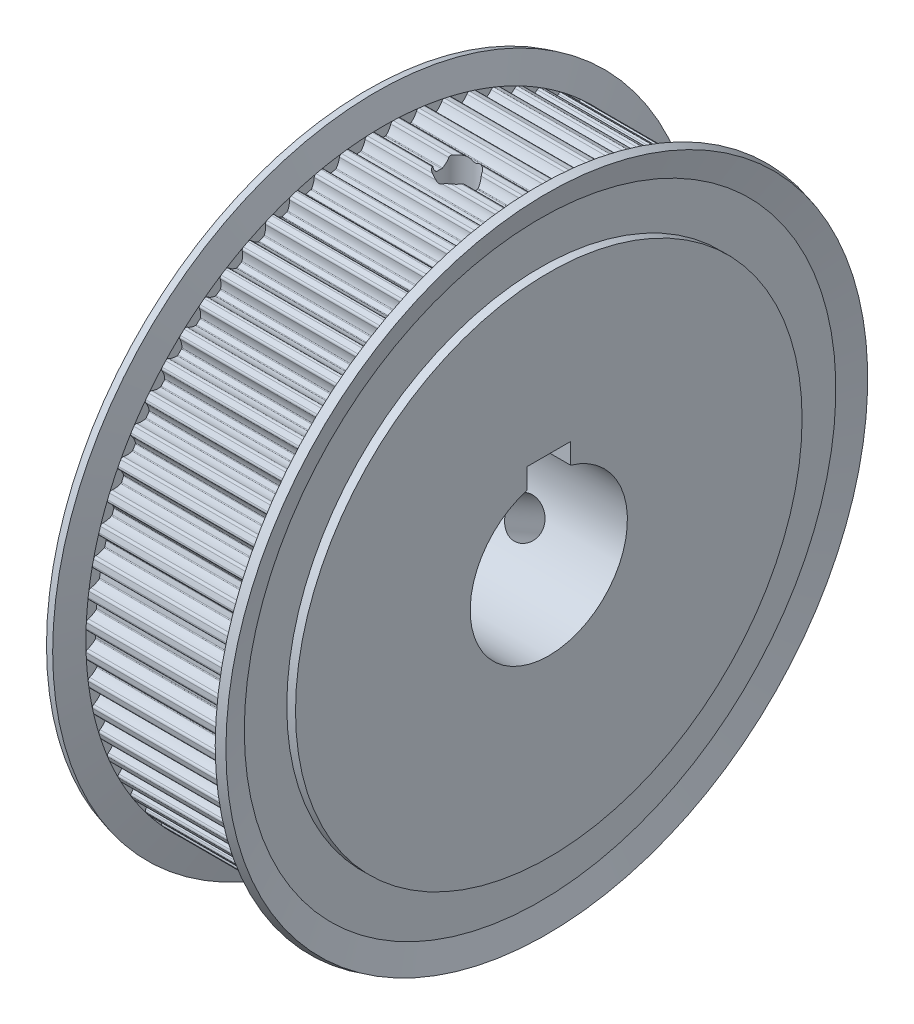
SolidWorks part; units mm, degrees
ref_plane "正面" through (0, 0, 0) normal (0, 0, 1) x (1, 0, 0)
ref_plane "平面" through (0, 0, 0) normal (0, 1, 0) x (1, 0, 0)
ref_plane "右側面" through (0, 0, 0) normal (1, 0, 0) x (0, 0, -1)
ref_plane "平面1" through (0, 0, 0) normal (0, 0, 1) x (1, 0, 0)
sketch "ｽｹｯﾁ1" plane through (0, 0, 0) normal (0, 0, 1) x (1, 0, 0)
  line L0 (0, 0) -> (0, 29)
  line L1 (0, 29) -> (1, 29)
  line L2 (1, 29) -> (1, 33.8633)
  line L3 (1, 33.8633) -> (0.2289, 36.7412)
  line L4 (0.2289, 36.7412) -> (1.1948, 37)
  line L5 (1.1948, 37) -> (2, 33.995)
  line L6 (2, 33.995) -> (19, 33.995)
  line L7 (19, 33.995) -> (19.8052, 37)
  line L8 (19.8052, 37) -> (20.7711, 36.7412)
  line L9 (20.7711, 36.7412) -> (20, 33.8633)
  line L10 (20, 33.8633) -> (20, 29)
  line L11 (20, 29) -> (21, 29)
  line L12 (21, 29) -> (21, 0)
  line L13 (21, 0) -> (0, 0)
  line L14 (21, 0) -> (0, 0) construction
revolve "回転1" add sketch "ｽｹｯﾁ1" angle 360 about L14
ref_plane "平面2" through (0, 0, 0) normal (0, 0, 1) x (1, 0, 0)
sketch "ｽｹｯﾁ2" plane through (0, 0, 0) normal (0, 0, 1) x (1, 0, 0)
  line L0 (0, 0) -> (0, 9)
  line L1 (0, 9) -> (21, 9)
  line L2 (21, 9) -> (21, 0)
  line L3 (21, 0) -> (0, 0)
  line L4 (21, 0) -> (0, 0) construction
revolve "ｶｯﾄ - 回転1" cut sketch "ｽｹｯﾁ2" angle 360 about L4
ref_plane "平面3" through (2, 0, 0) normal (1, 0, 0) x (0, 0, -1)
sketch "ｽｹｯﾁ3" plane through (2, 0, 0) normal (1, 0, 0) x (0, 0, -1)
  circle A0 centre (0, 0) radius 38.995
  arc A1 (-33.7772, -0.9117) -> (-33.9742, -1.189) centre (-33.6944, -1.1792) ccw
  arc A2 (-33.9742, -1.189) -> (-33.9485, -1.7766) centre (0, 0) ccw
  arc A3 (-33.9485, -1.7766) -> (-33.7281, -2.0357) centre (-33.6689, -1.762) ccw
  arc A4 (-33.7281, -2.0357) -> (-32.8326, -2.4906) centre (-34.1454, -3.9661) cw
  arc A5 (-32.8326, -2.4906) -> (-32.7828, -2.5908) centre (-32.9323, -2.6026) cw
  arc A6 (-32.7828, -2.5908) -> (-32.7346, -3.1412) centre (0, 0) ccw
  arc A7 (-32.7346, -3.1412) -> (-32.7663, -3.2486) centre (-32.8839, -3.1556) cw
  arc A8 (-32.7663, -3.2486) -> (-33.5692, -3.8521) centre (-34.3154, -2.0235) cw
  arc A9 (-33.5692, -3.8521) -> (-33.7413, -4.1455) centre (-33.4634, -4.1113) ccw
  arc A10 (-33.7413, -4.1455) -> (-33.6645, -4.7287) centre (0, 0) ccw
  arc A11 (-33.6645, -4.7287) -> (-33.4223, -4.9675) centre (-33.3872, -4.6897) ccw
  arc A12 (-33.4223, -4.9675) -> (-32.4906, -5.3426) centre (-33.6698, -6.9269) cw
  arc A13 (-32.4906, -5.3426) -> (-32.4322, -5.4382) centre (-32.5802, -5.463) cw
  arc A14 (-32.4322, -5.4382) -> (-32.3363, -5.9823) centre (0, 0) ccw
  arc A15 (-32.3363, -5.9823) -> (-32.3585, -6.092) centre (-32.4838, -6.0096) cw
  arc A16 (-32.3585, -6.092) -> (-33.1057, -6.7632) centre (-34.0085, -5.0066) cw
  arc A17 (-33.1057, -6.7632) -> (-33.2516, -7.0704) centre (-32.9777, -7.0122) ccw
  arc A18 (-33.2516, -7.0704) -> (-33.1243, -7.6447) centre (0, 0) ccw
  arc A19 (-33.1243, -7.6447) -> (-32.8622, -7.8616) centre (-32.8515, -7.5818) ccw
  arc A20 (-32.8622, -7.8616) -> (-31.9013, -8.154) centre (-32.938, -9.8351) cw
  arc A21 (-31.9013, -8.154) -> (-31.8349, -8.2441) centre (-31.9801, -8.2817) cw
  arc A22 (-31.8349, -8.2441) -> (-31.6918, -8.7778) centre (0, 0) ccw
  arc A23 (-31.6918, -8.7778) -> (-31.7044, -8.8891) centre (-31.8364, -8.8178) cw
  arc A24 (-31.7044, -8.8891) -> (-32.3903, -9.6228) centre (-33.4427, -7.9515) cw
  arc A25 (-32.3903, -9.6228) -> (-32.5088, -9.9416) centre (-32.2411, -9.8597) ccw
  arc A26 (-32.5088, -9.9416) -> (-32.332, -10.5026) centre (0, 0) ccw
  arc A27 (-32.332, -10.5026) -> (-32.052, -10.6958) centre (-32.0657, -10.4161) ccw
  arc A28 (-32.052, -10.6958) -> (-31.0693, -10.9034) centre (-31.9555, -12.6684) cw
  arc A29 (-31.0693, -10.9034) -> (-30.9952, -10.9873) centre (-31.1366, -11.0375) cw
  arc A30 (-30.9952, -10.9873) -> (-30.8062, -11.5065) centre (0, 0) ccw
  arc A31 (-30.8062, -11.5065) -> (-30.809, -11.6184) centre (-30.9467, -11.559) cw
  arc A32 (-30.809, -11.6184) -> (-31.4283, -12.4092) centre (-32.6224, -10.836) cw
  arc A33 (-31.4283, -12.4092) -> (-31.5187, -12.7371) centre (-31.2591, -12.6322) ccw
  arc A34 (-31.5187, -12.7371) -> (-31.2936, -13.2806) centre (0, 0) ccw
  arc A35 (-31.2936, -13.2806) -> (-30.9978, -13.4486) centre (-31.0358, -13.1712) ccw
  arc A36 (-30.9978, -13.4486) -> (-30.0007, -13.5698) centre (-30.7297, -15.4053) cw
  arc A37 (-30.0007, -13.5698) -> (-29.9196, -13.6469) centre (-30.0561, -13.7092) cw
  arc A38 (-29.9196, -13.6469) -> (-29.6861, -14.1477) centre (0, 0) ccw
  arc A39 (-29.6861, -14.1477) -> (-29.6792, -14.2594) centre (-29.8215, -14.2122) cw
  arc A40 (-29.6792, -14.2594) -> (-30.2272, -15.1011) centre (-31.5538, -13.638) cw
  arc A41 (-30.2272, -15.1011) -> (-30.2886, -15.4357) centre (-30.0391, -15.3085) ccw
  arc A42 (-30.2886, -15.4357) -> (-30.017, -15.9574) centre (0, 0) ccw
  arc A43 (-30.017, -15.9574) -> (-29.7077, -16.099) centre (-29.7698, -15.826) ccw
  arc A44 (-29.7077, -16.099) -> (-28.7039, -16.1329) centre (-29.2701, -18.025) cw
  arc A45 (-28.7039, -16.1329) -> (-28.6164, -16.2027) centre (-28.7469, -16.2766) cw
  arc A46 (-28.6164, -16.2027) -> (-28.3401, -16.6812) centre (0, 0) ccw
  arc A47 (-28.3401, -16.6812) -> (-28.3234, -16.7919) centre (-28.4694, -16.7573) cw
  arc A48 (-28.3234, -16.7919) -> (-28.796, -17.6781) centre (-30.2451, -16.3362) cw
  arc A49 (-28.796, -17.6781) -> (-28.828, -18.0168) centre (-28.5906, -17.8684) ccw
  arc A50 (-28.828, -18.0168) -> (-28.512, -18.5129) centre (0, 0) ccw
  arc A51 (-28.512, -18.5129) -> (-28.1916, -18.627) centre (-28.2772, -18.3604) ccw
  arc A52 (-28.1916, -18.627) -> (-27.1886, -18.5732) centre (-27.5878, -20.5074) cw
  arc A53 (-27.1886, -18.5732) -> (-27.0953, -18.6351) centre (-27.2189, -18.7201) cw
  arc A54 (-27.0953, -18.6351) -> (-26.7784, -19.0877) centre (0, 0) ccw
  arc A55 (-26.7784, -19.0877) -> (-26.7521, -19.1965) centre (-26.9006, -19.1748) cw
  arc A56 (-26.7521, -19.1965) -> (-27.1457, -20.1206) centre (-28.7063, -18.9101) cw
  arc A57 (-27.1457, -20.1206) -> (-27.1481, -20.4607) centre (-26.9245, -20.2922) ccw
  arc A58 (-27.1481, -20.4607) -> (-26.79, -20.9274) centre (0, 0) ccw
  arc A59 (-26.79, -20.9274) -> (-26.4608, -21.0132) centre (-26.5693, -20.755) ccw
  arc A60 (-26.4608, -21.0132) -> (-25.4664, -20.8722) centre (-25.6955, -22.8338) cw
  arc A61 (-25.4664, -20.8722) -> (-25.3681, -20.9257) centre (-25.4838, -21.0211) cw
  arc A62 (-25.3681, -20.9257) -> (-25.0129, -21.349) centre (0, 0) ccw
  arc A63 (-25.0129, -21.349) -> (-24.9773, -21.4551) centre (-25.127, -21.4463) cw
  arc A64 (-24.9773, -21.4551) -> (-25.2888, -22.4099) centre (-26.9489, -21.34) cw
  arc A65 (-25.2888, -22.4099) -> (-25.2615, -22.749) centre (-25.0534, -22.5616) ccw
  arc A66 (-25.2615, -22.749) -> (-24.8641, -23.1827) centre (0, 0) ccw
  arc A67 (-24.8641, -23.1827) -> (-24.5287, -23.2394) centre (-24.6593, -22.9917) ccw
  arc A68 (-24.5287, -23.2394) -> (-23.5503, -23.0123) centre (-23.6076, -24.9864) cw
  arc A69 (-23.5503, -23.0123) -> (-23.4477, -23.057) centre (-23.5547, -23.1622) cw
  arc A70 (-23.4477, -23.057) -> (-23.057, -23.4477) centre (0, 0) ccw
  arc A71 (-23.057, -23.4477) -> (-23.0123, -23.5503) centre (-23.1622, -23.5547) cw
  arc A72 (-23.0123, -23.5503) -> (-23.2394, -24.5287) centre (-24.9864, -23.6076) cw
  arc A73 (-23.2394, -24.5287) -> (-23.1827, -24.8641) centre (-22.9917, -24.6593) ccw
  arc A74 (-23.1827, -24.8641) -> (-22.749, -25.2615) centre (0, 0) ccw
  arc A75 (-22.749, -25.2615) -> (-22.4099, -25.2888) centre (-22.5616, -25.0534) ccw
  arc A76 (-22.4099, -25.2888) -> (-21.4551, -24.9773) centre (-21.34, -26.9489) cw
  arc A77 (-21.4551, -24.9773) -> (-21.349, -25.0129) centre (-21.4463, -25.127) cw
  arc A78 (-21.349, -25.0129) -> (-20.9257, -25.3681) centre (0, 0) ccw
  arc A79 (-20.9257, -25.3681) -> (-20.8722, -25.4664) centre (-21.0211, -25.4838) cw
  arc A80 (-20.8722, -25.4664) -> (-21.0132, -26.4608) centre (-22.8338, -25.6955) cw
  arc A81 (-21.0132, -26.4608) -> (-20.9274, -26.79) centre (-20.755, -26.5693) ccw
  arc A82 (-20.9274, -26.79) -> (-20.4607, -27.1481) centre (0, 0) ccw
  arc A83 (-20.4607, -27.1481) -> (-20.1206, -27.1457) centre (-20.2922, -26.9245) ccw
  arc A84 (-20.1206, -27.1457) -> (-19.1965, -26.7521) centre (-18.9101, -28.7063) cw
  arc A85 (-19.1965, -26.7521) -> (-19.0877, -26.7784) centre (-19.1748, -26.9006) cw
  arc A86 (-19.0877, -26.7784) -> (-18.6351, -27.0953) centre (0, 0) ccw
  arc A87 (-18.6351, -27.0953) -> (-18.5732, -27.1886) centre (-18.7201, -27.2189) cw
  arc A88 (-18.5732, -27.1886) -> (-18.627, -28.1916) centre (-20.5074, -27.5878) cw
  arc A89 (-18.627, -28.1916) -> (-18.5129, -28.512) centre (-18.3604, -28.2772) ccw
  arc A90 (-18.5129, -28.512) -> (-18.0168, -28.828) centre (0, 0) ccw
  arc A91 (-18.0168, -28.828) -> (-17.6781, -28.796) centre (-17.8684, -28.5906) ccw
  arc A92 (-17.6781, -28.796) -> (-16.7919, -28.3234) centre (-16.3362, -30.2451) cw
  arc A93 (-16.7919, -28.3234) -> (-16.6812, -28.3401) centre (-16.7573, -28.4694) cw
  arc A94 (-16.6812, -28.3401) -> (-16.2027, -28.6164) centre (0, 0) ccw
  arc A95 (-16.2027, -28.6164) -> (-16.1329, -28.7039) centre (-16.2766, -28.7469) cw
  arc A96 (-16.1329, -28.7039) -> (-16.099, -29.7077) centre (-18.025, -29.2701) cw
  arc A97 (-16.099, -29.7077) -> (-15.9574, -30.017) centre (-15.826, -29.7698) ccw
  arc A98 (-15.9574, -30.017) -> (-15.4357, -30.2886) centre (0, 0) ccw
  arc A99 (-15.4357, -30.2886) -> (-15.1011, -30.2272) centre (-15.3085, -30.0391) ccw
  arc A100 (-15.1011, -30.2272) -> (-14.2594, -29.6792) centre (-13.638, -31.5538) cw
  arc A101 (-14.2594, -29.6792) -> (-14.1477, -29.6861) centre (-14.2122, -29.8215) cw
  arc A102 (-14.1477, -29.6861) -> (-13.6469, -29.9196) centre (0, 0) ccw
  arc A103 (-13.6469, -29.9196) -> (-13.5698, -30.0007) centre (-13.7092, -30.0561) cw
  arc A104 (-13.5698, -30.0007) -> (-13.4486, -30.9978) centre (-15.4053, -30.7297) cw
  arc A105 (-13.4486, -30.9978) -> (-13.2806, -31.2936) centre (-13.1712, -31.0358) ccw
  arc A106 (-13.2806, -31.2936) -> (-12.7371, -31.5187) centre (0, 0) ccw
  arc A107 (-12.7371, -31.5187) -> (-12.4092, -31.4283) centre (-12.6322, -31.2591) ccw
  arc A108 (-12.4092, -31.4283) -> (-11.6184, -30.809) centre (-10.836, -32.6224) cw
  arc A109 (-11.6184, -30.809) -> (-11.5065, -30.8062) centre (-11.559, -30.9467) cw
  arc A110 (-11.5065, -30.8062) -> (-10.9873, -30.9952) centre (0, 0) ccw
  arc A111 (-10.9873, -30.9952) -> (-10.9034, -31.0693) centre (-11.0375, -31.1366) cw
  arc A112 (-10.9034, -31.0693) -> (-10.6958, -32.052) centre (-12.6684, -31.9555) cw
  arc A113 (-10.6958, -32.052) -> (-10.5026, -32.332) centre (-10.4161, -32.0657) ccw
  arc A114 (-10.5026, -32.332) -> (-9.9416, -32.5088) centre (0, 0) ccw
  arc A115 (-9.9416, -32.5088) -> (-9.6228, -32.3903) centre (-9.8597, -32.2411) ccw
  arc A116 (-9.6228, -32.3903) -> (-8.8891, -31.7044) centre (-7.9515, -33.4427) cw
  arc A117 (-8.8891, -31.7044) -> (-8.7778, -31.6918) centre (-8.8178, -31.8364) cw
  arc A118 (-8.7778, -31.6918) -> (-8.2441, -31.8349) centre (0, 0) ccw
  arc A119 (-8.2441, -31.8349) -> (-8.154, -31.9013) centre (-8.2817, -31.9801) cw
  arc A120 (-8.154, -31.9013) -> (-7.8616, -32.8622) centre (-9.8351, -32.938) cw
  arc A121 (-7.8616, -32.8622) -> (-7.6447, -33.1243) centre (-7.5818, -32.8515) ccw
  arc A122 (-7.6447, -33.1243) -> (-7.0704, -33.2516) centre (0, 0) ccw
  arc A123 (-7.0704, -33.2516) -> (-6.7632, -33.1057) centre (-7.0122, -32.9777) ccw
  arc A124 (-6.7632, -33.1057) -> (-6.092, -32.3585) centre (-5.0066, -34.0085) cw
  arc A125 (-6.092, -32.3585) -> (-5.9823, -32.3363) centre (-6.0096, -32.4838) cw
  arc A126 (-5.9823, -32.3363) -> (-5.4382, -32.4322) centre (0, 0) ccw
  arc A127 (-5.4382, -32.4322) -> (-5.3426, -32.4906) centre (-5.463, -32.5802) cw
  arc A128 (-5.3426, -32.4906) -> (-4.9675, -33.4223) centre (-6.9269, -33.6698) cw
  arc A129 (-4.9675, -33.4223) -> (-4.7287, -33.6645) centre (-4.6897, -33.3872) ccw
  arc A130 (-4.7287, -33.6645) -> (-4.1455, -33.7413) centre (0, 0) ccw
  arc A131 (-4.1455, -33.7413) -> (-3.8521, -33.5692) centre (-4.1113, -33.4634) ccw
  arc A132 (-3.8521, -33.5692) -> (-3.2486, -32.7663) centre (-2.0235, -34.3154) cw
  arc A133 (-3.2486, -32.7663) -> (-3.1412, -32.7346) centre (-3.1556, -32.8839) cw
  arc A134 (-3.1412, -32.7346) -> (-2.5908, -32.7828) centre (0, 0) ccw
  arc A135 (-2.5908, -32.7828) -> (-2.4906, -32.8326) centre (-2.6026, -32.9323) cw
  arc A136 (-2.4906, -32.8326) -> (-2.0357, -33.7281) centre (-3.9661, -34.1454) cw
  arc A137 (-2.0357, -33.7281) -> (-1.7766, -33.9485) centre (-1.762, -33.6689) ccw
  arc A138 (-1.7766, -33.9485) -> (-1.189, -33.9742) centre (0, 0) ccw
  arc A139 (-1.189, -33.9742) -> (-0.9117, -33.7772) centre (-1.1792, -33.6944) ccw
  arc A140 (-0.9117, -33.7772) -> (-0.3805, -32.9247) centre (0.975, -34.3612) cw
  arc A141 (-0.3805, -32.9247) -> (-0.2763, -32.8838) centre (-0.2775, -33.0338) cw
  arc A142 (-0.2763, -32.8838) -> (0.2763, -32.8838) centre (0, 0) ccw
  arc A143 (0.2763, -32.8838) -> (0.3805, -32.9247) centre (0.2775, -33.0338) cw
  arc A144 (0.3805, -32.9247) -> (0.9117, -33.7772) centre (-0.975, -34.3612) cw
  arc A145 (0.9117, -33.7772) -> (1.189, -33.9742) centre (1.1792, -33.6944) ccw
  arc A146 (1.189, -33.9742) -> (1.7766, -33.9485) centre (0, 0) ccw
  arc A147 (1.7766, -33.9485) -> (2.0357, -33.7281) centre (1.762, -33.6689) ccw
  arc A148 (2.0357, -33.7281) -> (2.4906, -32.8326) centre (3.9661, -34.1454) cw
  arc A149 (2.4906, -32.8326) -> (2.5908, -32.7828) centre (2.6026, -32.9323) cw
  arc A150 (2.5908, -32.7828) -> (3.1412, -32.7346) centre (0, 0) ccw
  arc A151 (3.1412, -32.7346) -> (3.2486, -32.7663) centre (3.1556, -32.8839) cw
  arc A152 (3.2486, -32.7663) -> (3.8521, -33.5692) centre (2.0235, -34.3154) cw
  arc A153 (3.8521, -33.5692) -> (4.1455, -33.7413) centre (4.1113, -33.4634) ccw
  arc A154 (4.1455, -33.7413) -> (4.7287, -33.6645) centre (0, 0) ccw
  arc A155 (4.7287, -33.6645) -> (4.9675, -33.4223) centre (4.6897, -33.3872) ccw
  arc A156 (4.9675, -33.4223) -> (5.3426, -32.4906) centre (6.9269, -33.6698) cw
  arc A157 (5.3426, -32.4906) -> (5.4382, -32.4322) centre (5.463, -32.5802) cw
  arc A158 (5.4382, -32.4322) -> (5.9823, -32.3363) centre (0, 0) ccw
  arc A159 (5.9823, -32.3363) -> (6.092, -32.3585) centre (6.0096, -32.4838) cw
  arc A160 (6.092, -32.3585) -> (6.7632, -33.1057) centre (5.0066, -34.0085) cw
  arc A161 (6.7632, -33.1057) -> (7.0704, -33.2516) centre (7.0122, -32.9777) ccw
  arc A162 (7.0704, -33.2516) -> (7.6447, -33.1243) centre (0, 0) ccw
  arc A163 (7.6447, -33.1243) -> (7.8616, -32.8622) centre (7.5818, -32.8515) ccw
  arc A164 (7.8616, -32.8622) -> (8.154, -31.9013) centre (9.8351, -32.938) cw
  arc A165 (8.154, -31.9013) -> (8.2441, -31.8349) centre (8.2817, -31.9801) cw
  arc A166 (8.2441, -31.8349) -> (8.7778, -31.6918) centre (0, 0) ccw
  arc A167 (8.7778, -31.6918) -> (8.8891, -31.7044) centre (8.8178, -31.8364) cw
  arc A168 (8.8891, -31.7044) -> (9.6228, -32.3903) centre (7.9515, -33.4427) cw
  arc A169 (9.6228, -32.3903) -> (9.9416, -32.5088) centre (9.8597, -32.2411) ccw
  arc A170 (9.9416, -32.5088) -> (10.5026, -32.332) centre (0, 0) ccw
  arc A171 (10.5026, -32.332) -> (10.6958, -32.052) centre (10.4161, -32.0657) ccw
  arc A172 (10.6958, -32.052) -> (10.9034, -31.0693) centre (12.6684, -31.9555) cw
  arc A173 (10.9034, -31.0693) -> (10.9873, -30.9952) centre (11.0375, -31.1366) cw
  arc A174 (10.9873, -30.9952) -> (11.5065, -30.8062) centre (0, 0) ccw
  arc A175 (11.5065, -30.8062) -> (11.6184, -30.809) centre (11.559, -30.9467) cw
  arc A176 (11.6184, -30.809) -> (12.4092, -31.4283) centre (10.836, -32.6224) cw
  arc A177 (12.4092, -31.4283) -> (12.7371, -31.5187) centre (12.6322, -31.2591) ccw
  arc A178 (12.7371, -31.5187) -> (13.2806, -31.2936) centre (0, 0) ccw
  arc A179 (13.2806, -31.2936) -> (13.4486, -30.9978) centre (13.1712, -31.0358) ccw
  arc A180 (13.4486, -30.9978) -> (13.5698, -30.0007) centre (15.4053, -30.7297) cw
  arc A181 (13.5698, -30.0007) -> (13.6469, -29.9196) centre (13.7092, -30.0561) cw
  arc A182 (13.6469, -29.9196) -> (14.1477, -29.6861) centre (0, 0) ccw
  arc A183 (14.1477, -29.6861) -> (14.2594, -29.6792) centre (14.2122, -29.8215) cw
  arc A184 (14.2594, -29.6792) -> (15.1011, -30.2272) centre (13.638, -31.5538) cw
  arc A185 (15.1011, -30.2272) -> (15.4357, -30.2886) centre (15.3085, -30.0391) ccw
  arc A186 (15.4357, -30.2886) -> (15.9574, -30.017) centre (0, 0) ccw
  arc A187 (15.9574, -30.017) -> (16.099, -29.7077) centre (15.826, -29.7698) ccw
  arc A188 (16.099, -29.7077) -> (16.1329, -28.7039) centre (18.025, -29.2701) cw
  arc A189 (16.1329, -28.7039) -> (16.2027, -28.6164) centre (16.2766, -28.7469) cw
  arc A190 (16.2027, -28.6164) -> (16.6812, -28.3401) centre (0, 0) ccw
  arc A191 (16.6812, -28.3401) -> (16.7919, -28.3234) centre (16.7573, -28.4694) cw
  arc A192 (16.7919, -28.3234) -> (17.6781, -28.796) centre (16.3362, -30.2451) cw
  arc A193 (17.6781, -28.796) -> (18.0168, -28.828) centre (17.8684, -28.5906) ccw
  arc A194 (18.0168, -28.828) -> (18.5129, -28.512) centre (0, 0) ccw
  arc A195 (18.5129, -28.512) -> (18.627, -28.1916) centre (18.3604, -28.2772) ccw
  arc A196 (18.627, -28.1916) -> (18.5732, -27.1886) centre (20.5074, -27.5878) cw
  arc A197 (18.5732, -27.1886) -> (18.6351, -27.0953) centre (18.7201, -27.2189) cw
  arc A198 (18.6351, -27.0953) -> (19.0877, -26.7784) centre (0, 0) ccw
  arc A199 (19.0877, -26.7784) -> (19.1965, -26.7521) centre (19.1748, -26.9006) cw
  arc A200 (19.1965, -26.7521) -> (20.1206, -27.1457) centre (18.9101, -28.7063) cw
  arc A201 (20.1206, -27.1457) -> (20.4607, -27.1481) centre (20.2922, -26.9245) ccw
  arc A202 (20.4607, -27.1481) -> (20.9274, -26.79) centre (0, 0) ccw
  arc A203 (20.9274, -26.79) -> (21.0132, -26.4608) centre (20.755, -26.5693) ccw
  arc A204 (21.0132, -26.4608) -> (20.8722, -25.4664) centre (22.8338, -25.6955) cw
  arc A205 (20.8722, -25.4664) -> (20.9257, -25.3681) centre (21.0211, -25.4838) cw
  arc A206 (20.9257, -25.3681) -> (21.349, -25.0129) centre (0, 0) ccw
  arc A207 (21.349, -25.0129) -> (21.4551, -24.9773) centre (21.4463, -25.127) cw
  arc A208 (21.4551, -24.9773) -> (22.4099, -25.2888) centre (21.34, -26.9489) cw
  arc A209 (22.4099, -25.2888) -> (22.749, -25.2615) centre (22.5616, -25.0534) ccw
  arc A210 (22.749, -25.2615) -> (23.1827, -24.8641) centre (0, 0) ccw
  arc A211 (23.1827, -24.8641) -> (23.2394, -24.5287) centre (22.9917, -24.6593) ccw
  arc A212 (23.2394, -24.5287) -> (23.0123, -23.5503) centre (24.9864, -23.6076) cw
  arc A213 (23.0123, -23.5503) -> (23.057, -23.4477) centre (23.1622, -23.5547) cw
  arc A214 (23.057, -23.4477) -> (23.4477, -23.057) centre (0, 0) ccw
  arc A215 (23.4477, -23.057) -> (23.5503, -23.0123) centre (23.5547, -23.1622) cw
  arc A216 (23.5503, -23.0123) -> (24.5287, -23.2394) centre (23.6076, -24.9864) cw
  arc A217 (24.5287, -23.2394) -> (24.8641, -23.1827) centre (24.6593, -22.9917) ccw
  arc A218 (24.8641, -23.1827) -> (25.2615, -22.749) centre (0, 0) ccw
  arc A219 (25.2615, -22.749) -> (25.2888, -22.4099) centre (25.0534, -22.5616) ccw
  arc A220 (25.2888, -22.4099) -> (24.9773, -21.4551) centre (26.9489, -21.34) cw
  arc A221 (24.9773, -21.4551) -> (25.0129, -21.349) centre (25.127, -21.4463) cw
  arc A222 (25.0129, -21.349) -> (25.3681, -20.9257) centre (0, 0) ccw
  arc A223 (25.3681, -20.9257) -> (25.4664, -20.8722) centre (25.4838, -21.0211) cw
  arc A224 (25.4664, -20.8722) -> (26.4608, -21.0132) centre (25.6955, -22.8338) cw
  arc A225 (26.4608, -21.0132) -> (26.79, -20.9274) centre (26.5693, -20.755) ccw
  arc A226 (26.79, -20.9274) -> (27.1481, -20.4607) centre (0, 0) ccw
  arc A227 (27.1481, -20.4607) -> (27.1457, -20.1206) centre (26.9245, -20.2922) ccw
  arc A228 (27.1457, -20.1206) -> (26.7521, -19.1965) centre (28.7063, -18.9101) cw
  arc A229 (26.7521, -19.1965) -> (26.7784, -19.0877) centre (26.9006, -19.1748) cw
  arc A230 (26.7784, -19.0877) -> (27.0953, -18.6351) centre (0, 0) ccw
  arc A231 (27.0953, -18.6351) -> (27.1886, -18.5732) centre (27.2189, -18.7201) cw
  arc A232 (27.1886, -18.5732) -> (28.1916, -18.627) centre (27.5878, -20.5074) cw
  arc A233 (28.1916, -18.627) -> (28.512, -18.5129) centre (28.2772, -18.3604) ccw
  arc A234 (28.512, -18.5129) -> (28.828, -18.0168) centre (0, 0) ccw
  arc A235 (28.828, -18.0168) -> (28.796, -17.6781) centre (28.5906, -17.8684) ccw
  arc A236 (28.796, -17.6781) -> (28.3234, -16.7919) centre (30.2451, -16.3362) cw
  arc A237 (28.3234, -16.7919) -> (28.3401, -16.6812) centre (28.4694, -16.7573) cw
  arc A238 (28.3401, -16.6812) -> (28.6164, -16.2027) centre (0, 0) ccw
  arc A239 (28.6164, -16.2027) -> (28.7039, -16.1329) centre (28.7469, -16.2766) cw
  arc A240 (28.7039, -16.1329) -> (29.7077, -16.099) centre (29.2701, -18.025) cw
  arc A241 (29.7077, -16.099) -> (30.017, -15.9574) centre (29.7698, -15.826) ccw
  arc A242 (30.017, -15.9574) -> (30.2886, -15.4357) centre (0, 0) ccw
  arc A243 (30.2886, -15.4357) -> (30.2272, -15.1011) centre (30.0391, -15.3085) ccw
  arc A244 (30.2272, -15.1011) -> (29.6792, -14.2594) centre (31.5538, -13.638) cw
  arc A245 (29.6792, -14.2594) -> (29.6861, -14.1477) centre (29.8215, -14.2122) cw
  arc A246 (29.6861, -14.1477) -> (29.9196, -13.6469) centre (0, 0) ccw
  arc A247 (29.9196, -13.6469) -> (30.0007, -13.5698) centre (30.0561, -13.7092) cw
  arc A248 (30.0007, -13.5698) -> (30.9978, -13.4486) centre (30.7297, -15.4053) cw
  arc A249 (30.9978, -13.4486) -> (31.2936, -13.2806) centre (31.0358, -13.1712) ccw
  arc A250 (31.2936, -13.2806) -> (31.5187, -12.7371) centre (0, 0) ccw
  arc A251 (31.5187, -12.7371) -> (31.4283, -12.4092) centre (31.2591, -12.6322) ccw
  arc A252 (31.4283, -12.4092) -> (30.809, -11.6184) centre (32.6224, -10.836) cw
  arc A253 (30.809, -11.6184) -> (30.8062, -11.5065) centre (30.9467, -11.559) cw
  arc A254 (30.8062, -11.5065) -> (30.9952, -10.9873) centre (0, 0) ccw
  arc A255 (30.9952, -10.9873) -> (31.0693, -10.9034) centre (31.1366, -11.0375) cw
  arc A256 (31.0693, -10.9034) -> (32.052, -10.6958) centre (31.9555, -12.6684) cw
  arc A257 (32.052, -10.6958) -> (32.332, -10.5026) centre (32.0657, -10.4161) ccw
  arc A258 (32.332, -10.5026) -> (32.5088, -9.9416) centre (0, 0) ccw
  arc A259 (32.5088, -9.9416) -> (32.3903, -9.6228) centre (32.2411, -9.8597) ccw
  arc A260 (32.3903, -9.6228) -> (31.7044, -8.8891) centre (33.4427, -7.9515) cw
  arc A261 (31.7044, -8.8891) -> (31.6918, -8.7778) centre (31.8364, -8.8178) cw
  arc A262 (31.6918, -8.7778) -> (31.8349, -8.2441) centre (0, 0) ccw
  arc A263 (31.8349, -8.2441) -> (31.9013, -8.154) centre (31.9801, -8.2817) cw
  arc A264 (31.9013, -8.154) -> (32.8622, -7.8616) centre (32.938, -9.8351) cw
  arc A265 (32.8622, -7.8616) -> (33.1243, -7.6447) centre (32.8515, -7.5818) ccw
  arc A266 (33.1243, -7.6447) -> (33.2516, -7.0704) centre (0, 0) ccw
  arc A267 (33.2516, -7.0704) -> (33.1057, -6.7632) centre (32.9777, -7.0122) ccw
  arc A268 (33.1057, -6.7632) -> (32.3585, -6.092) centre (34.0085, -5.0066) cw
  arc A269 (32.3585, -6.092) -> (32.3363, -5.9823) centre (32.4838, -6.0096) cw
  arc A270 (32.3363, -5.9823) -> (32.4322, -5.4382) centre (0, 0) ccw
  arc A271 (32.4322, -5.4382) -> (32.4906, -5.3426) centre (32.5802, -5.463) cw
  arc A272 (32.4906, -5.3426) -> (33.4223, -4.9675) centre (33.6698, -6.9269) cw
  arc A273 (33.4223, -4.9675) -> (33.6645, -4.7287) centre (33.3872, -4.6897) ccw
  arc A274 (33.6645, -4.7287) -> (33.7413, -4.1455) centre (0, 0) ccw
  arc A275 (33.7413, -4.1455) -> (33.5692, -3.8521) centre (33.4634, -4.1113) ccw
  arc A276 (33.5692, -3.8521) -> (32.7663, -3.2486) centre (34.3154, -2.0235) cw
  arc A277 (32.7663, -3.2486) -> (32.7346, -3.1412) centre (32.8839, -3.1556) cw
  arc A278 (32.7346, -3.1412) -> (32.7828, -2.5908) centre (0, 0) ccw
  arc A279 (32.7828, -2.5908) -> (32.8326, -2.4906) centre (32.9323, -2.6026) cw
  arc A280 (32.8326, -2.4906) -> (33.7281, -2.0357) centre (34.1454, -3.9661) cw
  arc A281 (33.7281, -2.0357) -> (33.9485, -1.7766) centre (33.6689, -1.762) ccw
  arc A282 (33.9485, -1.7766) -> (33.9742, -1.189) centre (0, 0) ccw
  arc A283 (33.9742, -1.189) -> (33.7772, -0.9117) centre (33.6944, -1.1792) ccw
  arc A284 (33.7772, -0.9117) -> (32.9247, -0.3805) centre (34.3612, 0.975) cw
  arc A285 (32.9247, -0.3805) -> (32.8838, -0.2763) centre (33.0338, -0.2775) cw
  arc A286 (32.8838, -0.2763) -> (32.8838, 0.2763) centre (0, 0) ccw
  arc A287 (32.8838, 0.2763) -> (32.9247, 0.3805) centre (33.0338, 0.2775) cw
  arc A288 (32.9247, 0.3805) -> (33.7772, 0.9117) centre (34.3612, -0.975) cw
  arc A289 (33.7772, 0.9117) -> (33.9742, 1.189) centre (33.6944, 1.1792) ccw
  arc A290 (33.9742, 1.189) -> (33.9485, 1.7766) centre (0, 0) ccw
  arc A291 (33.9485, 1.7766) -> (33.7281, 2.0357) centre (33.6689, 1.762) ccw
  arc A292 (33.7281, 2.0357) -> (32.8326, 2.4906) centre (34.1454, 3.9661) cw
  arc A293 (32.8326, 2.4906) -> (32.7828, 2.5908) centre (32.9323, 2.6026) cw
  arc A294 (32.7828, 2.5908) -> (32.7346, 3.1412) centre (0, 0) ccw
  arc A295 (32.7346, 3.1412) -> (32.7663, 3.2486) centre (32.8839, 3.1556) cw
  arc A296 (32.7663, 3.2486) -> (33.5692, 3.8521) centre (34.3154, 2.0235) cw
  arc A297 (33.5692, 3.8521) -> (33.7413, 4.1455) centre (33.4634, 4.1113) ccw
  arc A298 (33.7413, 4.1455) -> (33.6645, 4.7287) centre (0, 0) ccw
  arc A299 (33.6645, 4.7287) -> (33.4223, 4.9675) centre (33.3872, 4.6897) ccw
  arc A300 (33.4223, 4.9675) -> (32.4906, 5.3426) centre (33.6698, 6.9269) cw
  arc A301 (32.4906, 5.3426) -> (32.4322, 5.4382) centre (32.5802, 5.463) cw
  arc A302 (32.4322, 5.4382) -> (32.3363, 5.9823) centre (0, 0) ccw
  arc A303 (32.3363, 5.9823) -> (32.3585, 6.092) centre (32.4838, 6.0096) cw
  arc A304 (32.3585, 6.092) -> (33.1057, 6.7632) centre (34.0085, 5.0066) cw
  arc A305 (33.1057, 6.7632) -> (33.2516, 7.0704) centre (32.9777, 7.0122) ccw
  arc A306 (33.2516, 7.0704) -> (33.1243, 7.6447) centre (0, 0) ccw
  arc A307 (33.1243, 7.6447) -> (32.8622, 7.8616) centre (32.8515, 7.5818) ccw
  arc A308 (32.8622, 7.8616) -> (31.9013, 8.154) centre (32.938, 9.8351) cw
  arc A309 (31.9013, 8.154) -> (31.8349, 8.2441) centre (31.9801, 8.2817) cw
  arc A310 (31.8349, 8.2441) -> (31.6918, 8.7778) centre (0, 0) ccw
  arc A311 (31.6918, 8.7778) -> (31.7044, 8.8891) centre (31.8364, 8.8178) cw
  arc A312 (31.7044, 8.8891) -> (32.3903, 9.6228) centre (33.4427, 7.9515) cw
  arc A313 (32.3903, 9.6228) -> (32.5088, 9.9416) centre (32.2411, 9.8597) ccw
  arc A314 (32.5088, 9.9416) -> (32.332, 10.5026) centre (0, 0) ccw
  arc A315 (32.332, 10.5026) -> (32.052, 10.6958) centre (32.0657, 10.4161) ccw
  arc A316 (32.052, 10.6958) -> (31.0693, 10.9034) centre (31.9555, 12.6684) cw
  arc A317 (31.0693, 10.9034) -> (30.9952, 10.9873) centre (31.1366, 11.0375) cw
  arc A318 (30.9952, 10.9873) -> (30.8062, 11.5065) centre (0, 0) ccw
  arc A319 (30.8062, 11.5065) -> (30.809, 11.6184) centre (30.9467, 11.559) cw
  arc A320 (30.809, 11.6184) -> (31.4283, 12.4092) centre (32.6224, 10.836) cw
  arc A321 (31.4283, 12.4092) -> (31.5187, 12.7371) centre (31.2591, 12.6322) ccw
  arc A322 (31.5187, 12.7371) -> (31.2936, 13.2806) centre (0, 0) ccw
  arc A323 (31.2936, 13.2806) -> (30.9978, 13.4486) centre (31.0358, 13.1712) ccw
  arc A324 (30.9978, 13.4486) -> (30.0007, 13.5698) centre (30.7297, 15.4053) cw
  arc A325 (30.0007, 13.5698) -> (29.9196, 13.6469) centre (30.0561, 13.7092) cw
  arc A326 (29.9196, 13.6469) -> (29.6861, 14.1477) centre (0, 0) ccw
  arc A327 (29.6861, 14.1477) -> (29.6792, 14.2594) centre (29.8215, 14.2122) cw
  arc A328 (29.6792, 14.2594) -> (30.2272, 15.1011) centre (31.5538, 13.638) cw
  arc A329 (30.2272, 15.1011) -> (30.2886, 15.4357) centre (30.0391, 15.3085) ccw
  arc A330 (30.2886, 15.4357) -> (30.017, 15.9574) centre (0, 0) ccw
  arc A331 (30.017, 15.9574) -> (29.7077, 16.099) centre (29.7698, 15.826) ccw
  arc A332 (29.7077, 16.099) -> (28.7039, 16.1329) centre (29.2701, 18.025) cw
  arc A333 (28.7039, 16.1329) -> (28.6164, 16.2027) centre (28.7469, 16.2766) cw
  arc A334 (28.6164, 16.2027) -> (28.3401, 16.6812) centre (0, 0) ccw
  arc A335 (28.3401, 16.6812) -> (28.3234, 16.7919) centre (28.4694, 16.7573) cw
  arc A336 (28.3234, 16.7919) -> (28.796, 17.6781) centre (30.2451, 16.3362) cw
  arc A337 (28.796, 17.6781) -> (28.828, 18.0168) centre (28.5906, 17.8684) ccw
  arc A338 (28.828, 18.0168) -> (28.512, 18.5129) centre (0, 0) ccw
  arc A339 (28.512, 18.5129) -> (28.1916, 18.627) centre (28.2772, 18.3604) ccw
  arc A340 (28.1916, 18.627) -> (27.1886, 18.5732) centre (27.5878, 20.5074) cw
  arc A341 (27.1886, 18.5732) -> (27.0953, 18.6351) centre (27.2189, 18.7201) cw
  arc A342 (27.0953, 18.6351) -> (26.7784, 19.0877) centre (0, 0) ccw
  arc A343 (26.7784, 19.0877) -> (26.7521, 19.1965) centre (26.9006, 19.1748) cw
  arc A344 (26.7521, 19.1965) -> (27.1457, 20.1206) centre (28.7063, 18.9101) cw
  arc A345 (27.1457, 20.1206) -> (27.1481, 20.4607) centre (26.9245, 20.2922) ccw
  arc A346 (27.1481, 20.4607) -> (26.79, 20.9274) centre (0, 0) ccw
  arc A347 (26.79, 20.9274) -> (26.4608, 21.0132) centre (26.5693, 20.755) ccw
  arc A348 (26.4608, 21.0132) -> (25.4664, 20.8722) centre (25.6955, 22.8338) cw
  arc A349 (25.4664, 20.8722) -> (25.3681, 20.9257) centre (25.4838, 21.0211) cw
  arc A350 (25.3681, 20.9257) -> (25.0129, 21.349) centre (0, 0) ccw
  arc A351 (25.0129, 21.349) -> (24.9773, 21.4551) centre (25.127, 21.4463) cw
  arc A352 (24.9773, 21.4551) -> (25.2888, 22.4099) centre (26.9489, 21.34) cw
  arc A353 (25.2888, 22.4099) -> (25.2615, 22.749) centre (25.0534, 22.5616) ccw
  arc A354 (25.2615, 22.749) -> (24.8641, 23.1827) centre (0, 0) ccw
  arc A355 (24.8641, 23.1827) -> (24.5287, 23.2394) centre (24.6593, 22.9917) ccw
  arc A356 (24.5287, 23.2394) -> (23.5503, 23.0123) centre (23.6076, 24.9864) cw
  arc A357 (23.5503, 23.0123) -> (23.4477, 23.057) centre (23.5547, 23.1622) cw
  arc A358 (23.4477, 23.057) -> (23.057, 23.4477) centre (0, 0) ccw
  arc A359 (23.057, 23.4477) -> (23.0123, 23.5503) centre (23.1622, 23.5547) cw
  arc A360 (23.0123, 23.5503) -> (23.2394, 24.5287) centre (24.9864, 23.6076) cw
  arc A361 (23.2394, 24.5287) -> (23.1827, 24.8641) centre (22.9917, 24.6593) ccw
  arc A362 (23.1827, 24.8641) -> (22.749, 25.2615) centre (0, 0) ccw
  arc A363 (22.749, 25.2615) -> (22.4099, 25.2888) centre (22.5616, 25.0534) ccw
  arc A364 (22.4099, 25.2888) -> (21.4551, 24.9773) centre (21.34, 26.9489) cw
  arc A365 (21.4551, 24.9773) -> (21.349, 25.0129) centre (21.4463, 25.127) cw
  arc A366 (21.349, 25.0129) -> (20.9257, 25.3681) centre (0, 0) ccw
  arc A367 (20.9257, 25.3681) -> (20.8722, 25.4664) centre (21.0211, 25.4838) cw
  arc A368 (20.8722, 25.4664) -> (21.0132, 26.4608) centre (22.8338, 25.6955) cw
  arc A369 (21.0132, 26.4608) -> (20.9274, 26.79) centre (20.755, 26.5693) ccw
  arc A370 (20.9274, 26.79) -> (20.4607, 27.1481) centre (0, 0) ccw
  arc A371 (20.4607, 27.1481) -> (20.1206, 27.1457) centre (20.2922, 26.9245) ccw
  arc A372 (20.1206, 27.1457) -> (19.1965, 26.7521) centre (18.9101, 28.7063) cw
  arc A373 (19.1965, 26.7521) -> (19.0877, 26.7784) centre (19.1748, 26.9006) cw
  arc A374 (19.0877, 26.7784) -> (18.6351, 27.0953) centre (0, 0) ccw
  arc A375 (18.6351, 27.0953) -> (18.5732, 27.1886) centre (18.7201, 27.2189) cw
  arc A376 (18.5732, 27.1886) -> (18.627, 28.1916) centre (20.5074, 27.5878) cw
  arc A377 (18.627, 28.1916) -> (18.5129, 28.512) centre (18.3604, 28.2772) ccw
  arc A378 (18.5129, 28.512) -> (18.0168, 28.828) centre (0, 0) ccw
  arc A379 (18.0168, 28.828) -> (17.6781, 28.796) centre (17.8684, 28.5906) ccw
  arc A380 (17.6781, 28.796) -> (16.7919, 28.3234) centre (16.3362, 30.2451) cw
  arc A381 (16.7919, 28.3234) -> (16.6812, 28.3401) centre (16.7573, 28.4694) cw
  arc A382 (16.6812, 28.3401) -> (16.2027, 28.6164) centre (0, 0) ccw
  arc A383 (16.2027, 28.6164) -> (16.1329, 28.7039) centre (16.2766, 28.7469) cw
  arc A384 (16.1329, 28.7039) -> (16.099, 29.7077) centre (18.025, 29.2701) cw
  arc A385 (16.099, 29.7077) -> (15.9574, 30.017) centre (15.826, 29.7698) ccw
  arc A386 (15.9574, 30.017) -> (15.4357, 30.2886) centre (0, 0) ccw
  arc A387 (15.4357, 30.2886) -> (15.1011, 30.2272) centre (15.3085, 30.0391) ccw
  arc A388 (15.1011, 30.2272) -> (14.2594, 29.6792) centre (13.638, 31.5538) cw
  arc A389 (14.2594, 29.6792) -> (14.1477, 29.6861) centre (14.2122, 29.8215) cw
  arc A390 (14.1477, 29.6861) -> (13.6469, 29.9196) centre (0, 0) ccw
  arc A391 (13.6469, 29.9196) -> (13.5698, 30.0007) centre (13.7092, 30.0561) cw
  arc A392 (13.5698, 30.0007) -> (13.4486, 30.9978) centre (15.4053, 30.7297) cw
  arc A393 (13.4486, 30.9978) -> (13.2806, 31.2936) centre (13.1712, 31.0358) ccw
  arc A394 (13.2806, 31.2936) -> (12.7371, 31.5187) centre (0, 0) ccw
  arc A395 (12.7371, 31.5187) -> (12.4092, 31.4283) centre (12.6322, 31.2591) ccw
  arc A396 (12.4092, 31.4283) -> (11.6184, 30.809) centre (10.836, 32.6224) cw
  arc A397 (11.6184, 30.809) -> (11.5065, 30.8062) centre (11.559, 30.9467) cw
  arc A398 (11.5065, 30.8062) -> (10.9873, 30.9952) centre (0, 0) ccw
  arc A399 (10.9873, 30.9952) -> (10.9034, 31.0693) centre (11.0375, 31.1366) cw
  arc A400 (10.9034, 31.0693) -> (10.6958, 32.052) centre (12.6684, 31.9555) cw
  arc A401 (10.6958, 32.052) -> (10.5026, 32.332) centre (10.4161, 32.0657) ccw
  arc A402 (10.5026, 32.332) -> (9.9416, 32.5088) centre (0, 0) ccw
  arc A403 (9.9416, 32.5088) -> (9.6228, 32.3903) centre (9.8597, 32.2411) ccw
  arc A404 (9.6228, 32.3903) -> (8.8891, 31.7044) centre (7.9515, 33.4427) cw
  arc A405 (8.8891, 31.7044) -> (8.7778, 31.6918) centre (8.8178, 31.8364) cw
  arc A406 (8.7778, 31.6918) -> (8.2441, 31.8349) centre (0, 0) ccw
  arc A407 (8.2441, 31.8349) -> (8.154, 31.9013) centre (8.2817, 31.9801) cw
  arc A408 (8.154, 31.9013) -> (7.8616, 32.8622) centre (9.8351, 32.938) cw
  arc A409 (7.8616, 32.8622) -> (7.6447, 33.1243) centre (7.5818, 32.8515) ccw
  arc A410 (7.6447, 33.1243) -> (7.0704, 33.2516) centre (0, 0) ccw
  arc A411 (7.0704, 33.2516) -> (6.7632, 33.1057) centre (7.0122, 32.9777) ccw
  arc A412 (6.7632, 33.1057) -> (6.092, 32.3585) centre (5.0066, 34.0085) cw
  arc A413 (6.092, 32.3585) -> (5.9823, 32.3363) centre (6.0096, 32.4838) cw
  arc A414 (5.9823, 32.3363) -> (5.4382, 32.4322) centre (0, 0) ccw
  arc A415 (5.4382, 32.4322) -> (5.3426, 32.4906) centre (5.463, 32.5802) cw
  arc A416 (5.3426, 32.4906) -> (4.9675, 33.4223) centre (6.9269, 33.6698) cw
  arc A417 (4.9675, 33.4223) -> (4.7287, 33.6645) centre (4.6897, 33.3872) ccw
  arc A418 (4.7287, 33.6645) -> (4.1455, 33.7413) centre (0, 0) ccw
  arc A419 (4.1455, 33.7413) -> (3.8521, 33.5692) centre (4.1113, 33.4634) ccw
  arc A420 (3.8521, 33.5692) -> (3.2486, 32.7663) centre (2.0235, 34.3154) cw
  arc A421 (3.2486, 32.7663) -> (3.1412, 32.7346) centre (3.1556, 32.8839) cw
  arc A422 (3.1412, 32.7346) -> (2.5908, 32.7828) centre (0, 0) ccw
  arc A423 (2.5908, 32.7828) -> (2.4906, 32.8326) centre (2.6026, 32.9323) cw
  arc A424 (2.4906, 32.8326) -> (2.0357, 33.7281) centre (3.9661, 34.1454) cw
  arc A425 (2.0357, 33.7281) -> (1.7766, 33.9485) centre (1.762, 33.6689) ccw
  arc A426 (1.7766, 33.9485) -> (1.189, 33.9742) centre (0, 0) ccw
  arc A427 (1.189, 33.9742) -> (0.9117, 33.7772) centre (1.1792, 33.6944) ccw
  arc A428 (0.9117, 33.7772) -> (0.3805, 32.9247) centre (-0.975, 34.3612) cw
  arc A429 (0.3805, 32.9247) -> (0.2763, 32.8838) centre (0.2775, 33.0338) cw
  arc A430 (0.2763, 32.8838) -> (-0.2763, 32.8838) centre (0, 0) ccw
  arc A431 (-0.2763, 32.8838) -> (-0.3805, 32.9247) centre (-0.2775, 33.0338) cw
  arc A432 (-0.3805, 32.9247) -> (-0.9117, 33.7772) centre (0.975, 34.3612) cw
  arc A433 (-0.9117, 33.7772) -> (-1.189, 33.9742) centre (-1.1792, 33.6944) ccw
  arc A434 (-1.189, 33.9742) -> (-1.7766, 33.9485) centre (0, 0) ccw
  arc A435 (-1.7766, 33.9485) -> (-2.0357, 33.7281) centre (-1.762, 33.6689) ccw
  arc A436 (-2.0357, 33.7281) -> (-2.4906, 32.8326) centre (-3.9661, 34.1454) cw
  arc A437 (-2.4906, 32.8326) -> (-2.5908, 32.7828) centre (-2.6026, 32.9323) cw
  arc A438 (-2.5908, 32.7828) -> (-3.1412, 32.7346) centre (0, 0) ccw
  arc A439 (-3.1412, 32.7346) -> (-3.2486, 32.7663) centre (-3.1556, 32.8839) cw
  arc A440 (-3.2486, 32.7663) -> (-3.8521, 33.5692) centre (-2.0235, 34.3154) cw
  arc A441 (-3.8521, 33.5692) -> (-4.1455, 33.7413) centre (-4.1113, 33.4634) ccw
  arc A442 (-4.1455, 33.7413) -> (-4.7287, 33.6645) centre (0, 0) ccw
  arc A443 (-4.7287, 33.6645) -> (-4.9675, 33.4223) centre (-4.6897, 33.3872) ccw
  arc A444 (-4.9675, 33.4223) -> (-5.3426, 32.4906) centre (-6.9269, 33.6698) cw
  arc A445 (-5.3426, 32.4906) -> (-5.4382, 32.4322) centre (-5.463, 32.5802) cw
  arc A446 (-5.4382, 32.4322) -> (-5.9823, 32.3363) centre (0, 0) ccw
  arc A447 (-5.9823, 32.3363) -> (-6.092, 32.3585) centre (-6.0096, 32.4838) cw
  arc A448 (-6.092, 32.3585) -> (-6.7632, 33.1057) centre (-5.0066, 34.0085) cw
  arc A449 (-6.7632, 33.1057) -> (-7.0704, 33.2516) centre (-7.0122, 32.9777) ccw
  arc A450 (-7.0704, 33.2516) -> (-7.6447, 33.1243) centre (0, 0) ccw
  arc A451 (-7.6447, 33.1243) -> (-7.8616, 32.8622) centre (-7.5818, 32.8515) ccw
  arc A452 (-7.8616, 32.8622) -> (-8.154, 31.9013) centre (-9.8351, 32.938) cw
  arc A453 (-8.154, 31.9013) -> (-8.2441, 31.8349) centre (-8.2817, 31.9801) cw
  arc A454 (-8.2441, 31.8349) -> (-8.7778, 31.6918) centre (0, 0) ccw
  arc A455 (-8.7778, 31.6918) -> (-8.8891, 31.7044) centre (-8.8178, 31.8364) cw
  arc A456 (-8.8891, 31.7044) -> (-9.6228, 32.3903) centre (-7.9515, 33.4427) cw
  arc A457 (-9.6228, 32.3903) -> (-9.9416, 32.5088) centre (-9.8597, 32.2411) ccw
  arc A458 (-9.9416, 32.5088) -> (-10.5026, 32.332) centre (0, 0) ccw
  arc A459 (-10.5026, 32.332) -> (-10.6958, 32.052) centre (-10.4161, 32.0657) ccw
  arc A460 (-10.6958, 32.052) -> (-10.9034, 31.0693) centre (-12.6684, 31.9555) cw
  arc A461 (-10.9034, 31.0693) -> (-10.9873, 30.9952) centre (-11.0375, 31.1366) cw
  arc A462 (-10.9873, 30.9952) -> (-11.5065, 30.8062) centre (0, 0) ccw
  arc A463 (-11.5065, 30.8062) -> (-11.6184, 30.809) centre (-11.559, 30.9467) cw
  arc A464 (-11.6184, 30.809) -> (-12.4092, 31.4283) centre (-10.836, 32.6224) cw
  arc A465 (-12.4092, 31.4283) -> (-12.7371, 31.5187) centre (-12.6322, 31.2591) ccw
  arc A466 (-12.7371, 31.5187) -> (-13.2806, 31.2936) centre (0, 0) ccw
  arc A467 (-13.2806, 31.2936) -> (-13.4486, 30.9978) centre (-13.1712, 31.0358) ccw
  arc A468 (-13.4486, 30.9978) -> (-13.5698, 30.0007) centre (-15.4053, 30.7297) cw
  arc A469 (-13.5698, 30.0007) -> (-13.6469, 29.9196) centre (-13.7092, 30.0561) cw
  arc A470 (-13.6469, 29.9196) -> (-14.1477, 29.6861) centre (0, 0) ccw
  arc A471 (-14.1477, 29.6861) -> (-14.2594, 29.6792) centre (-14.2122, 29.8215) cw
  arc A472 (-14.2594, 29.6792) -> (-15.1011, 30.2272) centre (-13.638, 31.5538) cw
  arc A473 (-15.1011, 30.2272) -> (-15.4357, 30.2886) centre (-15.3085, 30.0391) ccw
  arc A474 (-15.4357, 30.2886) -> (-15.9574, 30.017) centre (0, 0) ccw
  arc A475 (-15.9574, 30.017) -> (-16.099, 29.7077) centre (-15.826, 29.7698) ccw
  arc A476 (-16.099, 29.7077) -> (-16.1329, 28.7039) centre (-18.025, 29.2701) cw
  arc A477 (-16.1329, 28.7039) -> (-16.2027, 28.6164) centre (-16.2766, 28.7469) cw
  arc A478 (-16.2027, 28.6164) -> (-16.6812, 28.3401) centre (0, 0) ccw
  arc A479 (-16.6812, 28.3401) -> (-16.7919, 28.3234) centre (-16.7573, 28.4694) cw
  arc A480 (-16.7919, 28.3234) -> (-17.6781, 28.796) centre (-16.3362, 30.2451) cw
  arc A481 (-17.6781, 28.796) -> (-18.0168, 28.828) centre (-17.8684, 28.5906) ccw
  arc A482 (-18.0168, 28.828) -> (-18.5129, 28.512) centre (0, 0) ccw
  arc A483 (-18.5129, 28.512) -> (-18.627, 28.1916) centre (-18.3604, 28.2772) ccw
  arc A484 (-18.627, 28.1916) -> (-18.5732, 27.1886) centre (-20.5074, 27.5878) cw
  arc A485 (-18.5732, 27.1886) -> (-18.6351, 27.0953) centre (-18.7201, 27.2189) cw
  arc A486 (-18.6351, 27.0953) -> (-19.0877, 26.7784) centre (0, 0) ccw
  arc A487 (-19.0877, 26.7784) -> (-19.1965, 26.7521) centre (-19.1748, 26.9006) cw
  arc A488 (-19.1965, 26.7521) -> (-20.1206, 27.1457) centre (-18.9101, 28.7063) cw
  arc A489 (-20.1206, 27.1457) -> (-20.4607, 27.1481) centre (-20.2922, 26.9245) ccw
  arc A490 (-20.4607, 27.1481) -> (-20.9274, 26.79) centre (0, 0) ccw
  arc A491 (-20.9274, 26.79) -> (-21.0132, 26.4608) centre (-20.755, 26.5693) ccw
  arc A492 (-21.0132, 26.4608) -> (-20.8722, 25.4664) centre (-22.8338, 25.6955) cw
  arc A493 (-20.8722, 25.4664) -> (-20.9257, 25.3681) centre (-21.0211, 25.4838) cw
  arc A494 (-20.9257, 25.3681) -> (-21.349, 25.0129) centre (0, 0) ccw
  arc A495 (-21.349, 25.0129) -> (-21.4551, 24.9773) centre (-21.4463, 25.127) cw
  arc A496 (-21.4551, 24.9773) -> (-22.4099, 25.2888) centre (-21.34, 26.9489) cw
  arc A497 (-22.4099, 25.2888) -> (-22.749, 25.2615) centre (-22.5616, 25.0534) ccw
  arc A498 (-22.749, 25.2615) -> (-23.1827, 24.8641) centre (0, 0) ccw
  arc A499 (-23.1827, 24.8641) -> (-23.2394, 24.5287) centre (-22.9917, 24.6593) ccw
  arc A500 (-23.2394, 24.5287) -> (-23.0123, 23.5503) centre (-24.9864, 23.6076) cw
  arc A501 (-23.0123, 23.5503) -> (-23.057, 23.4477) centre (-23.1622, 23.5547) cw
  arc A502 (-23.057, 23.4477) -> (-23.4477, 23.057) centre (0, 0) ccw
  arc A503 (-23.4477, 23.057) -> (-23.5503, 23.0123) centre (-23.5547, 23.1622) cw
  arc A504 (-23.5503, 23.0123) -> (-24.5287, 23.2394) centre (-23.6076, 24.9864) cw
  arc A505 (-24.5287, 23.2394) -> (-24.8641, 23.1827) centre (-24.6593, 22.9917) ccw
  arc A506 (-24.8641, 23.1827) -> (-25.2615, 22.749) centre (0, 0) ccw
  arc A507 (-25.2615, 22.749) -> (-25.2888, 22.4099) centre (-25.0534, 22.5616) ccw
  arc A508 (-25.2888, 22.4099) -> (-24.9773, 21.4551) centre (-26.9489, 21.34) cw
  arc A509 (-24.9773, 21.4551) -> (-25.0129, 21.349) centre (-25.127, 21.4463) cw
  arc A510 (-25.0129, 21.349) -> (-25.3681, 20.9257) centre (0, 0) ccw
  arc A511 (-25.3681, 20.9257) -> (-25.4664, 20.8722) centre (-25.4838, 21.0211) cw
  arc A512 (-25.4664, 20.8722) -> (-26.4608, 21.0132) centre (-25.6955, 22.8338) cw
  arc A513 (-26.4608, 21.0132) -> (-26.79, 20.9274) centre (-26.5693, 20.755) ccw
  arc A514 (-26.79, 20.9274) -> (-27.1481, 20.4607) centre (0, 0) ccw
  arc A515 (-27.1481, 20.4607) -> (-27.1457, 20.1206) centre (-26.9245, 20.2922) ccw
  arc A516 (-27.1457, 20.1206) -> (-26.7521, 19.1965) centre (-28.7063, 18.9101) cw
  arc A517 (-26.7521, 19.1965) -> (-26.7784, 19.0877) centre (-26.9006, 19.1748) cw
  arc A518 (-26.7784, 19.0877) -> (-27.0953, 18.6351) centre (0, 0) ccw
  arc A519 (-27.0953, 18.6351) -> (-27.1886, 18.5732) centre (-27.2189, 18.7201) cw
  arc A520 (-27.1886, 18.5732) -> (-28.1916, 18.627) centre (-27.5878, 20.5074) cw
  arc A521 (-28.1916, 18.627) -> (-28.512, 18.5129) centre (-28.2772, 18.3604) ccw
  arc A522 (-28.512, 18.5129) -> (-28.828, 18.0168) centre (0, 0) ccw
  arc A523 (-28.828, 18.0168) -> (-28.796, 17.6781) centre (-28.5906, 17.8684) ccw
  arc A524 (-28.796, 17.6781) -> (-28.3234, 16.7919) centre (-30.2451, 16.3362) cw
  arc A525 (-28.3234, 16.7919) -> (-28.3401, 16.6812) centre (-28.4694, 16.7573) cw
  arc A526 (-28.3401, 16.6812) -> (-28.6164, 16.2027) centre (0, 0) ccw
  arc A527 (-28.6164, 16.2027) -> (-28.7039, 16.1329) centre (-28.7469, 16.2766) cw
  arc A528 (-28.7039, 16.1329) -> (-29.7077, 16.099) centre (-29.2701, 18.025) cw
  arc A529 (-29.7077, 16.099) -> (-30.017, 15.9574) centre (-29.7698, 15.826) ccw
  arc A530 (-30.017, 15.9574) -> (-30.2886, 15.4357) centre (0, 0) ccw
  arc A531 (-30.2886, 15.4357) -> (-30.2272, 15.1011) centre (-30.0391, 15.3085) ccw
  arc A532 (-30.2272, 15.1011) -> (-29.6792, 14.2594) centre (-31.5538, 13.638) cw
  arc A533 (-29.6792, 14.2594) -> (-29.6861, 14.1477) centre (-29.8215, 14.2122) cw
  arc A534 (-29.6861, 14.1477) -> (-29.9196, 13.6469) centre (0, 0) ccw
  arc A535 (-29.9196, 13.6469) -> (-30.0007, 13.5698) centre (-30.0561, 13.7092) cw
  arc A536 (-30.0007, 13.5698) -> (-30.9978, 13.4486) centre (-30.7297, 15.4053) cw
  arc A537 (-30.9978, 13.4486) -> (-31.2936, 13.2806) centre (-31.0358, 13.1712) ccw
  arc A538 (-31.2936, 13.2806) -> (-31.5187, 12.7371) centre (0, 0) ccw
  arc A539 (-31.5187, 12.7371) -> (-31.4283, 12.4092) centre (-31.2591, 12.6322) ccw
  arc A540 (-31.4283, 12.4092) -> (-30.809, 11.6184) centre (-32.6224, 10.836) cw
  arc A541 (-30.809, 11.6184) -> (-30.8062, 11.5065) centre (-30.9467, 11.559) cw
  arc A542 (-30.8062, 11.5065) -> (-30.9952, 10.9873) centre (0, 0) ccw
  arc A543 (-30.9952, 10.9873) -> (-31.0693, 10.9034) centre (-31.1366, 11.0375) cw
  arc A544 (-31.0693, 10.9034) -> (-32.052, 10.6958) centre (-31.9555, 12.6684) cw
  arc A545 (-32.052, 10.6958) -> (-32.332, 10.5026) centre (-32.0657, 10.4161) ccw
  arc A546 (-32.332, 10.5026) -> (-32.5088, 9.9416) centre (0, 0) ccw
  arc A547 (-32.5088, 9.9416) -> (-32.3903, 9.6228) centre (-32.2411, 9.8597) ccw
  arc A548 (-32.3903, 9.6228) -> (-31.7044, 8.8891) centre (-33.4427, 7.9515) cw
  arc A549 (-31.7044, 8.8891) -> (-31.6918, 8.7778) centre (-31.8364, 8.8178) cw
  arc A550 (-31.6918, 8.7778) -> (-31.8349, 8.2441) centre (0, 0) ccw
  arc A551 (-31.8349, 8.2441) -> (-31.9013, 8.154) centre (-31.9801, 8.2817) cw
  arc A552 (-31.9013, 8.154) -> (-32.8622, 7.8616) centre (-32.938, 9.8351) cw
  arc A553 (-32.8622, 7.8616) -> (-33.1243, 7.6447) centre (-32.8515, 7.5818) ccw
  arc A554 (-33.1243, 7.6447) -> (-33.2516, 7.0704) centre (0, 0) ccw
  arc A555 (-33.2516, 7.0704) -> (-33.1057, 6.7632) centre (-32.9777, 7.0122) ccw
  arc A556 (-33.1057, 6.7632) -> (-32.3585, 6.092) centre (-34.0085, 5.0066) cw
  arc A557 (-32.3585, 6.092) -> (-32.3363, 5.9823) centre (-32.4838, 6.0096) cw
  arc A558 (-32.3363, 5.9823) -> (-32.4322, 5.4382) centre (0, 0) ccw
  arc A559 (-32.4322, 5.4382) -> (-32.4906, 5.3426) centre (-32.5802, 5.463) cw
  arc A560 (-32.4906, 5.3426) -> (-33.4223, 4.9675) centre (-33.6698, 6.9269) cw
  arc A561 (-33.4223, 4.9675) -> (-33.6645, 4.7287) centre (-33.3872, 4.6897) ccw
  arc A562 (-33.6645, 4.7287) -> (-33.7413, 4.1455) centre (0, 0) ccw
  arc A563 (-33.7413, 4.1455) -> (-33.5692, 3.8521) centre (-33.4634, 4.1113) ccw
  arc A564 (-33.5692, 3.8521) -> (-32.7663, 3.2486) centre (-34.3154, 2.0235) cw
  arc A565 (-32.7663, 3.2486) -> (-32.7346, 3.1412) centre (-32.8839, 3.1556) cw
  arc A566 (-32.7346, 3.1412) -> (-32.7828, 2.5908) centre (0, 0) ccw
  arc A567 (-32.7828, 2.5908) -> (-32.8326, 2.4906) centre (-32.9323, 2.6026) cw
  arc A568 (-32.8326, 2.4906) -> (-33.7281, 2.0357) centre (-34.1454, 3.9661) cw
  arc A569 (-33.7281, 2.0357) -> (-33.9485, 1.7766) centre (-33.6689, 1.762) ccw
  arc A570 (-33.9485, 1.7766) -> (-33.9742, 1.189) centre (0, 0) ccw
  arc A571 (-33.9742, 1.189) -> (-33.7772, 0.9117) centre (-33.6944, 1.1792) ccw
  arc A572 (-33.7772, 0.9117) -> (-32.9247, 0.3805) centre (-34.3612, -0.975) cw
  arc A573 (-32.9247, 0.3805) -> (-32.8838, 0.2763) centre (-33.0338, 0.2775) cw
  arc A574 (-32.8838, 0.2763) -> (-32.8838, -0.2763) centre (0, 0) ccw
  arc A575 (-32.8838, -0.2763) -> (-32.9247, -0.3805) centre (-33.0338, -0.2775) cw
  arc A576 (-32.9247, -0.3805) -> (-33.7772, -0.9117) centre (-34.3612, 0.975) cw
extrude "ｶｯﾄ - 押し出し1" cut sketch "ｽｹｯﾁ3" along normal blind 17
ref_plane "平面4" through (0, 0, 0) normal (1, 0, 0) x (0, 0, -1)
sketch "ｽｹｯﾁ4" plane through (0, 0, 0) normal (1, 0, 0) x (0, 0, -1)
  line L0 (-2.5, 11) -> (-2.5, 0)
  line L1 (-2.5, 0) -> (2.5, 0)
  line L2 (2.5, 0) -> (2.5, 11)
  line L3 (2.5, 11) -> (-2.5, 11)
extrude "ｶｯﾄ - 押し出し2" cut sketch "ｽｹｯﾁ4" along normal blind 21
ref_plane "平面5" through (10.5, 0, 0) normal (1, 0, 0) x (0, 0, -1)
sketch "ｽｹｯﾁ5" plane through (10.5, 0, 0) normal (1, 0, 0) x (0, 0, -1)
  line L0 (0, 33.995) -> (2.067, 33.995)
  line L1 (2.067, 33.995) -> (2.067, 0)
  line L2 (2.067, 0) -> (0, 0)
  line L3 (0, 0) -> (0, 33.995)
  line L4 (0, 0) -> (0, 33.995) construction
revolve "ｶｯﾄ - 回転2" cut sketch "ｽｹｯﾁ5" angle 360 about L4
ref_plane "平面6" through (10.5, 0, 0) normal (1, 0, 0) x (0, 0, -1)
sketch "ｽｹｯﾁ6" plane through (10.5, 0, 0) normal (1, 0, 0) x (0, 0, -1)
  line L0 (29.4405, -16.9975) -> (28.407, -18.7876)
  line L1 (28.407, -18.7876) -> (-1.0335, -1.7901)
  line L2 (-1.0335, -1.7901) -> (0, 0)
  line L3 (0, 0) -> (29.4405, -16.9975)
  line L4 (0, 0) -> (29.4405, -16.9975) construction
revolve "ｶｯﾄ - 回転3" cut sketch "ｽｹｯﾁ6" angle 360 about L4
